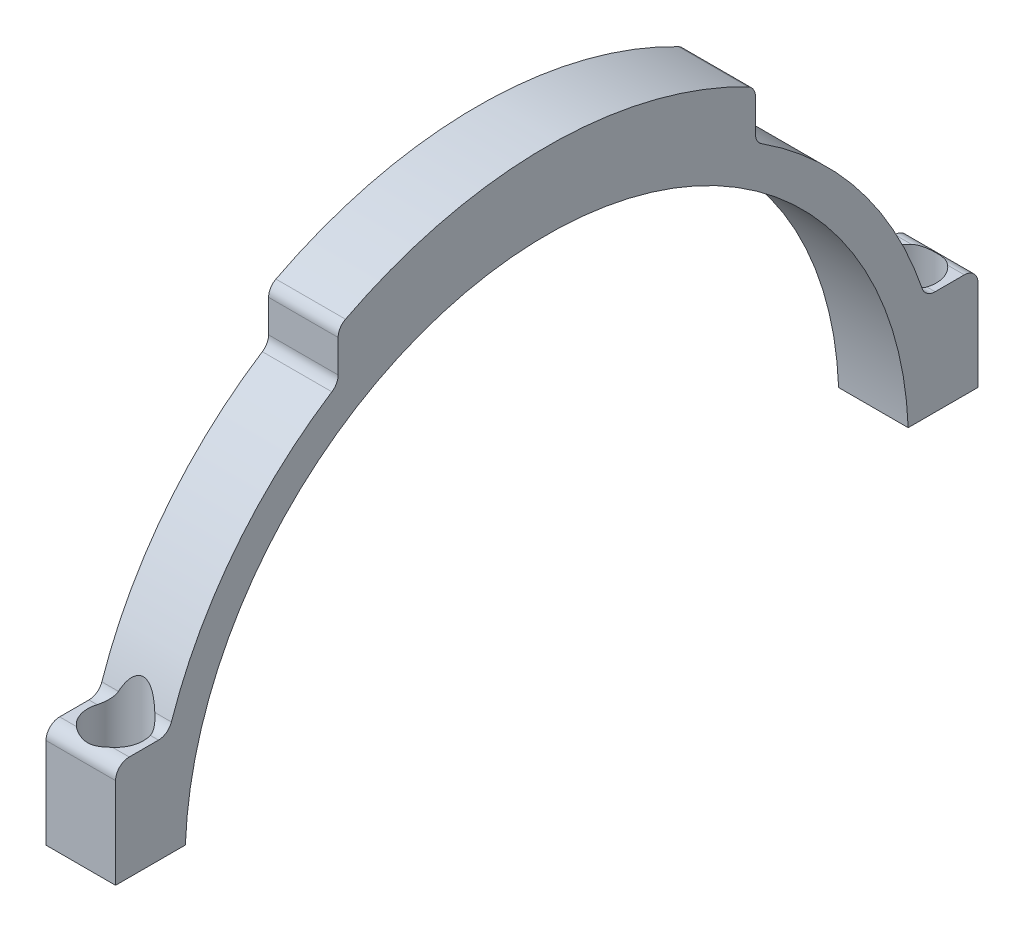
SolidWorks part; units mm, degrees
material "High Density Carbon Steel"
ref_plane "Front Plane" through (0, 0, 0) normal (0, 0, 1) x (1, 0, 0)
ref_plane "Top Plane" through (0, 0, 0) normal (0, 1, 0) x (1, 0, 0)
ref_plane "Right Plane" through (0, 0, 0) normal (1, 0, 0) x (0, 0, -1)
sketch "Sketch1" plane through (0, 0, 0) normal (1, 0, 0) x (0, 0, -1)
  line L1 (30, 49.5476) -> (30, 54.217)
  line L2 (-62, 2) -> (-51.9615, 2)
  line L3 (51.9615, 2) -> (62, 2)
  line L4 (-62, 2) -> (-62, 15.0376)
  line L5 (-60.0376, 17) -> (-55.83, 17)
  line L6 (62, 2) -> (62, 15.0376)
  line L7 (60.0376, 17) -> (55.83, 17)
  line L9 (-30, 49.5476) -> (-30, 54.217)
  arc A0 (51.9615, 2) -> (-51.9615, 2) centre (0, 0) ccw
  arc A1 (53.9719, 18.3313) -> (30.8986, 47.8986) centre (0, 0) ccw
  circle A2 centre (0, 0) radius 57 construction
  circle A3 centre (0, 0) radius 52 construction
  arc A4 (28.939, 55.9601) -> (-28.939, 55.9601) centre (0, 0) ccw
  arc A5 (60.1328, 18.7895) -> (-60.1328, 18.7895) centre (0, 0) ccw construction
  arc A6 (-30.8986, 47.8986) -> (-53.9719, 18.3313) centre (0, 0) ccw
  arc A7 (54.4059, 17) -> (-54.4059, 17) centre (0, 0) ccw construction
  arc A8 (-30.8986, 47.8986) -> (-30, 49.5476) centre (-31.9624, 49.5476) ccw
  arc A9 (-30, 54.217) -> (-28.939, 55.9601) centre (-28.0376, 54.217) cw
  arc A10 (30, 54.217) -> (28.939, 55.9601) centre (28.0376, 54.217) ccw
  arc A11 (30.8986, 47.8986) -> (30, 49.5476) centre (31.9624, 49.5476) cw
  arc A12 (-62, 15.0376) -> (-60.0376, 17) centre (-60.0376, 15.0376) cw
  arc A13 (-55.83, 17) -> (-53.9719, 18.3313) centre (-55.83, 18.9624) ccw
  arc A14 (62, 15.0376) -> (60.0376, 17) centre (60.0376, 15.0376) ccw
  arc A15 (55.83, 17) -> (53.9719, 18.3313) centre (55.83, 18.9624) cw
  point P14 (0, 52)
  dimension "D1" = 104
  dimension "D6" = 1.9624
  dimension "D2" = 6
  dimension "D3" = 30
  dimension "D4" = 30
  dimension "D5" = 5
extrude "Boss-Extrude1" add sketch "Sketch1" along normal blind 10
hole_wizard "CBORE for M4 Cheese Head Screw1" positions "Sketch5" profile "Sketch4" counterbore size "M4" standard "ISO"
sketch "Sketch5" plane through (0, 17, 0) normal (0, 1, 0) x (1, 0, 0)
  line L0 (10, 60.0376) -> (10, 55.83) construction
  line L1 (10, -62) -> (0, -62) construction
  line L2 (10, 62) -> (0, 62) construction
  line L4 (10, -55.83) -> (10, -60.0376) construction
  point P0 (5, 57)
  point P11 (5, -57)
  dimension "D1" = 5
  dimension "D2" = 5
  dimension "D3" = 5
  dimension "D4" = 5
sketch "Sketch4" plane through (5, 17, -57) normal (1, 0, 0) x (0, 0, 1)
  line L0 (0, 0) -> (0, 21.2919)
  line L1 (0, 21.2919) -> (2.15, 20)
  line L2 (2.15, 20) -> (2.15, 6.6)
  line L3 (2.15, 6.6) -> (4, 6.6)
  line L4 (4, 6.6) -> (4, 0)
  line L5 (4, 0) -> (0, 0)
  line L10 (0, 21.2919) -> (-2.15, 20) construction
  line L11 (0, -6.35) -> (0, 107.95) construction
  dimension "Hole Dia." = 4.3
  dimension "Hole Depth" = 20
  dimension "C'Bore Dia." = 8
  dimension "C'Bore Depth" = 6.6
  dimension "Drill Angle" = 118
sketch "Sketch6" plane through (0, 17, 0) normal (0, 1, 0) x (1, 0, 0)
  circle A0 centre (5, 57) radius 4
  circle A1 centre (5, -57) radius 4
extrude "Cut-Extrude1" cut sketch "Sketch6" along normal blind 8
